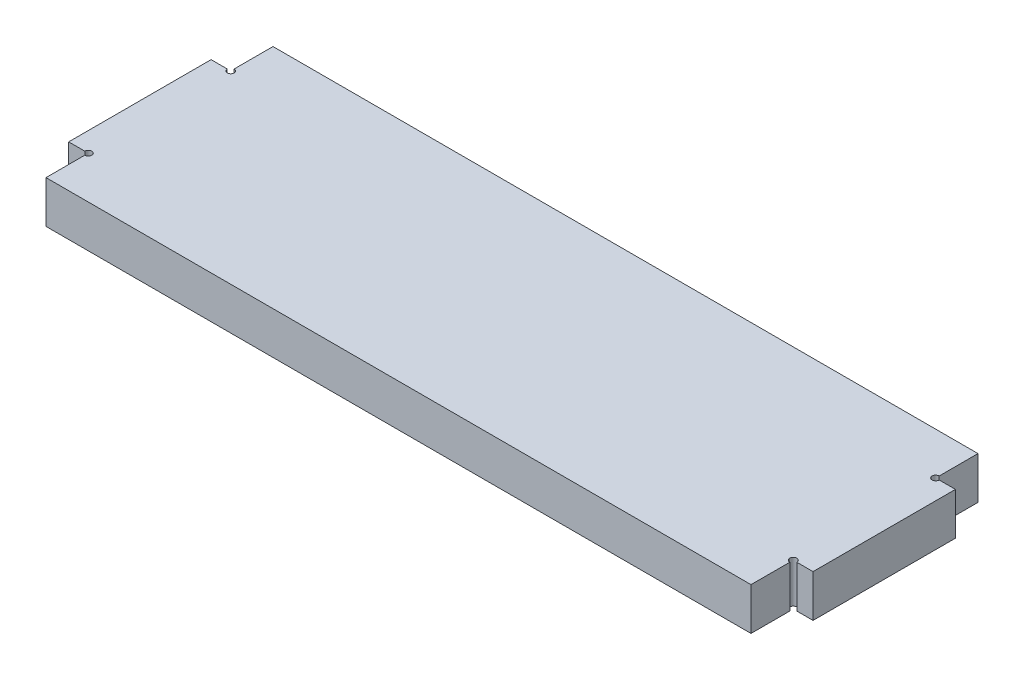
SolidWorks part; units mm, degrees
ref_plane "Front Plane" through (0, 0, 0) normal (0, 0, 1) x (1, 0, 0)
ref_plane "Top Plane" through (0, 0, 0) normal (0, 1, 0) x (1, 0, 0)
ref_plane "Right Plane" through (0, 0, 0) normal (1, 0, 0) x (0, 0, -1)
sketch "Sketch1" plane through (0, 0, 0) normal (0, 1, 0) x (1, 0, 0)
  line L0 (0.25, 5.3321) -> (1.4, 5.3321)
  line L1 (1.4, 5.3321) -> (1.4, -4.7679)
  line L2 (1.4, -4.7679) -> (0.25, -4.7679)
  line L3 (0, -5.0179) -> (0, -7.7679)
  line L4 (0, -7.7679) -> (-50, -7.7679)
  line L5 (0, 5.5821) -> (0, 8.3321)
  line L6 (0, 8.3321) -> (-50, 8.3321)
  line L7 (-50, 8.3321) -> (-50, 5.5774)
  line L8 (-50.2453, 5.3321) -> (-51.391, 5.3321)
  line L9 (-50, -7.7679) -> (-50, -5.0179)
  line L10 (-50.25, -4.7679) -> (-51.391, -4.7679)
  line L11 (-51.391, -4.7679) -> (-51.391, 5.3321)
  arc A0 (-50.2453, 5.3321) -> (-50, 5.5774) centre (-50, 5.3321) ccw
  arc A1 (-50, -5.0179) -> (-50.25, -4.7679) centre (-50, -4.7679) ccw
  arc A2 (0.25, -4.7679) -> (0, -5.0179) centre (0, -4.7679) ccw
  arc A3 (0, 5.5821) -> (0.25, 5.3321) centre (0, 5.3321) ccw
  dimension "D1" = 10.1
  dimension "D2" = 1.4
  dimension "D3" = 3
  dimension "D4" = 3
  dimension "D5" = 50
  dimension "D6" = 50
extrude "Boss-Extrude1" add sketch "Sketch1" along normal blind 3 contours L6 L7 A0 L8 L11 L10 A1 L9 L4 L3 A2 L2 L1 L0 A3 L5
